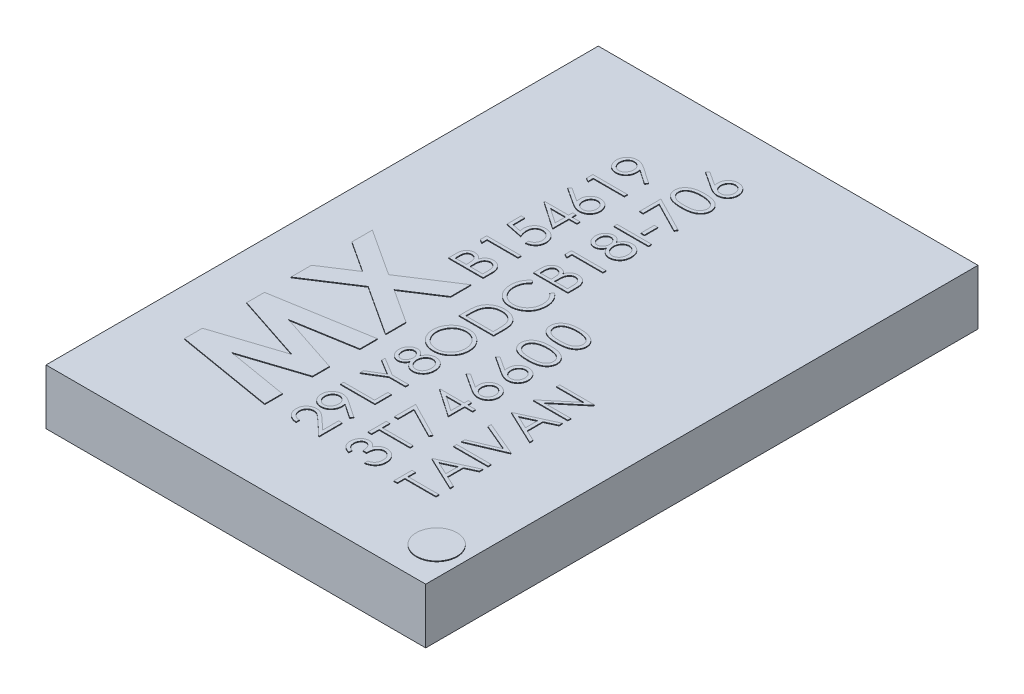
SolidWorks part; units mm, degrees
ref_plane "Plan de face" through (0, 0, 0) normal (0, 0, 1) x (1, 0, 0)
ref_plane "Plan de dessus" through (0, 0, 0) normal (0, 1, 0) x (1, 0, 0)
ref_plane "Plan de droite" through (0, 0, 0) normal (1, 0, 0) x (0, 0, -1)
sketch "Esquisse1" plane through (0, 0, 0) normal (0, 1, 0) x (1, 0, 0)
  line L1 (2.75, -4) -> (-2.75, -4)
  line L2 (2.75, -4) -> (2.75, 4)
  line L3 (2.75, 4) -> (-2.75, 4)
  line L4 (-2.75, -4) -> (-2.75, 4)
  line L5 (2.75, -4) -> (-2.75, 4) construction
  line L6 (2.75, 4) -> (-2.75, -4) construction
  point P0 (0, 0)
  dimension "D1" = 8
  dimension "D2" = 5.5
extrude "Boss.-Extru.1" add sketch "Esquisse1" along normal blind 0.8
sketch "Esquisse2" plane through (0, 0.8, 0) normal (0, 1, 0) x (1, 0, 0)
  line L0 (-0.6681, -2.9497) -> (-0.6681, 2.9497) construction
  line L1 (0.1319, -2.9497) -> (0.1319, 2.9497) construction
  line L2 (0.9319, -2.9497) -> (0.9319, 2.9497) construction
  line L3 (1.7319, -2.9497) -> (1.7319, 2.9497) construction
  line L4 (0, 0) -> (1.6726, 0) construction
  circle A0 centre (2.3409, -3.4321) radius 0.2945
  text T0 "MX" font "Century Gothic" height 1.4
  text T1 "                B154619\r\n" font "Century Gothic" height 0.5
  text T2 "TAIVAN" font "Century Gothic" height 0.5
  text T3 "29LY8ODCB18I-706" font "Century Gothic" height 0.5
  text T4 "3T746600" font "Century Gothic" height 0.5
  point P9 (1.7319, 0)
  dimension "D1" = 2.4
  dimension "D2" = 0.8
  dimension "D3" = 0.8
extrude "Boss.-Extru.2" add sketch "Esquisse2" along normal blind 0.01
